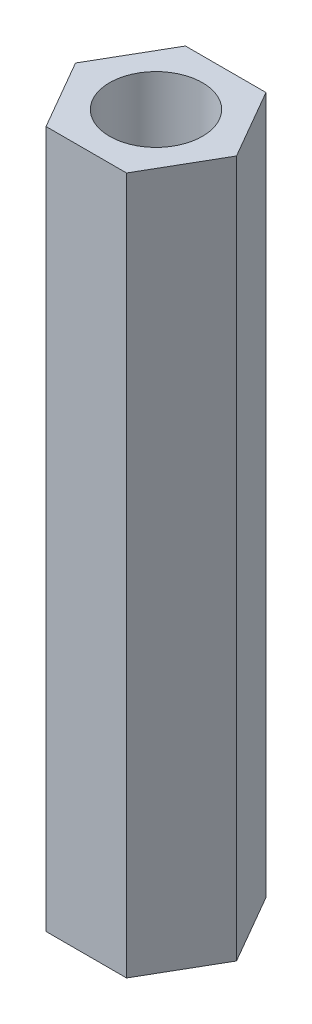
SolidWorks part; units mm, degrees
ref_plane "前视基准面" through (0, 0, 0) normal (0, 0, 1) x (1, 0, 0)
ref_plane "上视基准面" through (0, 0, 0) normal (0, 1, 0) x (1, 0, 0)
ref_plane "右视基准面" through (0, 0, 0) normal (1, 0, 0) x (0, 0, -1)
sketch "草图1" plane through (0, 0, 0) normal (0, 1, 0) x (1, 0, 0)
  line L1 (1.7321, 3) -> (-1.7321, 3)
  line L2 (-1.7321, 3) -> (-3.4641, 0)
  line L3 (-3.4641, 0) -> (-1.7321, -3)
  line L4 (-1.7321, -3) -> (1.7321, -3)
  line L5 (1.7321, -3) -> (3.4641, 0)
  line L6 (3.4641, 0) -> (1.7321, 3)
  circle A0 centre (0, 0) radius 3 construction
  circle A1 centre (0, 0) radius 2
  dimension "D1" = 6
  dimension "D2" = 4
extrude "凸台-拉伸1" add sketch "草图1" along normal blind 30
